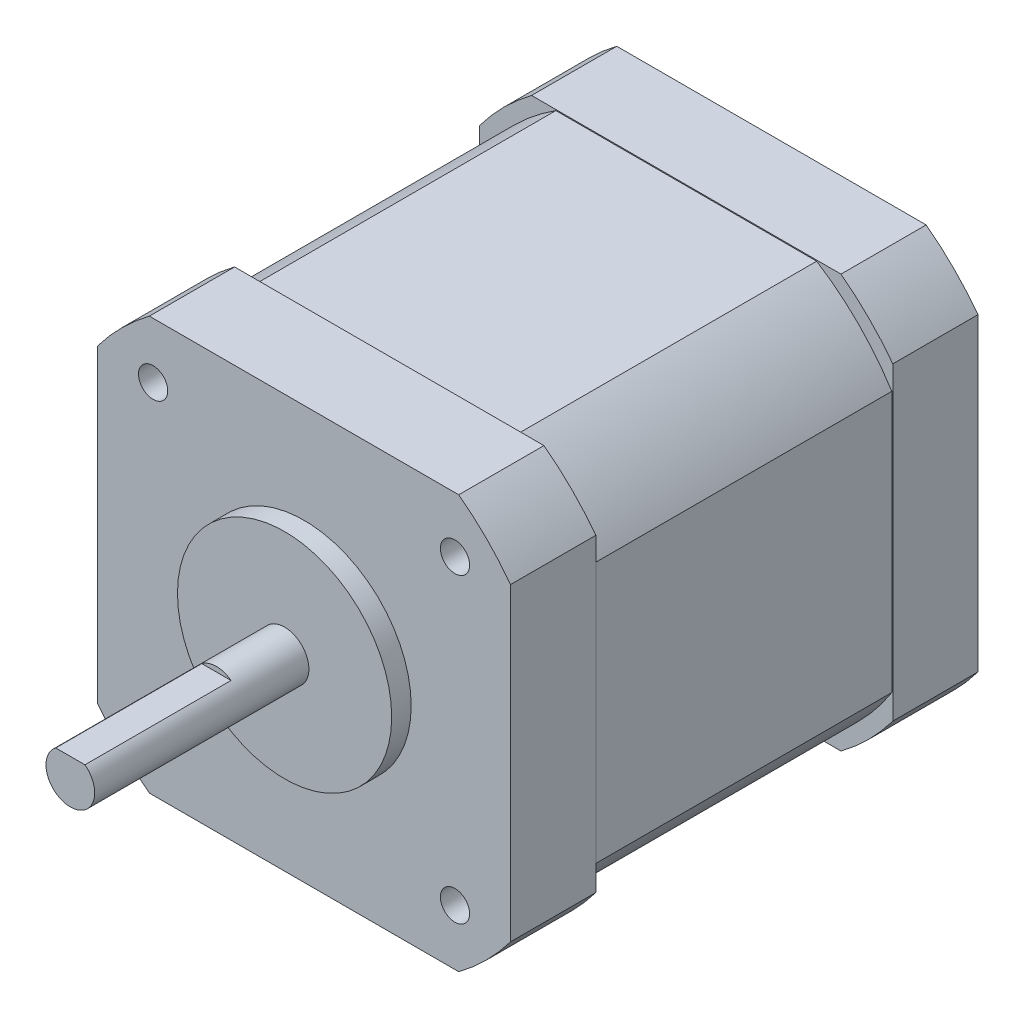
SolidWorks part; units mm, degrees
material "Plain Carbon Steel"
ref_plane "Front" through (0, 0, 0) normal (0, 0, 1) x (1, 0, 0)
ref_plane "Top" through (0, 0, 0) normal (0, 1, 0) x (1, 0, 0)
ref_plane "Right" through (0, 0, 0) normal (1, 0, 0) x (0, 0, -1)
sketch "Sketch1" plane through (0, 0, 0) normal (0, 0, 1) x (1, 0, 0)
  circle A0 centre (0, 0) radius 2.5
  dimension "D1" = 5
extrude "Boss-Extrude1" add sketch "Sketch1" along normal blind 24
sketch "Sketch2" plane through (0, 0, 0) normal (0, 0, -1) x (-1, 0, 0)
  circle A0 centre (0, 0) radius 11
  dimension "D1" = 22
extrude "Boss-Extrude2" add sketch "Sketch2" against normal blind 2
sketch "Sketch3" plane through (0, 0, 0) normal (0, 0, -1) x (-1, 0, 0)
  line L1 (21.209, -21.209) -> (-21.209, -21.209)
  line L2 (21.209, -21.209) -> (21.209, 21.209)
  line L3 (21.209, 21.209) -> (-21.209, 21.209)
  line L4 (-21.209, -21.209) -> (-21.209, 21.209)
  line L5 (21.209, -21.209) -> (-21.209, 21.209) construction
  line L6 (21.209, 21.209) -> (-21.209, -21.209) construction
  point P0 (0, 0)
  dimension "D1" = 42.418
extrude "Boss-Extrude3" add sketch "Sketch3" along normal blind 48
sketch "Sketch4" plane through (0, 0, -48) normal (0, 0, -1) x (-1, 0, 0)
  line L0 (-21.209, -15.888) -> (-21.209, -21.209)
  line L1 (15.888, -21.209) -> (21.209, -21.209)
  line L2 (21.209, 15.888) -> (21.209, 21.209)
  line L3 (-15.888, 21.209) -> (-21.209, 21.209)
  line L4 (-21.209, 21.209) -> (-21.209, -21.209)
  line L5 (-21.209, -21.209) -> (21.209, -21.209)
  line L6 (21.209, -21.209) -> (21.209, 21.209)
  line L7 (21.209, 21.209) -> (-21.209, 21.209)
  line L8 (-21.209, 21.209) -> (-21.209, 15.888)
  line L9 (-21.209, -21.209) -> (-15.888, -21.209)
  line L10 (21.209, -21.209) -> (21.209, -15.888)
  line L11 (21.209, 21.209) -> (15.888, 21.209)
  arc A0 (-21.209, -15.888) -> (-15.888, -21.209) centre (0, 0) ccw
  arc A1 (15.888, -21.209) -> (21.209, -15.888) centre (0, 0) ccw
  arc A2 (21.209, 15.888) -> (15.888, 21.209) centre (0, 0) ccw
  arc A3 (-15.888, 21.209) -> (-21.209, 15.888) centre (0, 0) ccw
  dimension "D2" = 26.5
  dimension "D1" = 0
extrude "Cut-Extrude1" cut sketch "Sketch4" against normal through all
hole_wizard "M3x0.5 Tapped Hole1" positions "Sketch6" profile "Sketch5" tap size "M3x0.5" standard "ANSI Metric"
sketch "Sketch6" plane through (0, 0, 0) normal (0, 0, 1) x (1, 0, 0)
  line L0 (-16.1632, 0) -> (0, 0) construction
  line L1 (0, 0) -> (0, 15.0764) construction
  point P0 (-15.5, 15.5)
  point P11 (-15.5, -15.5)
  point P12 (15.5, -15.5)
  point P13 (15.5, 15.5)
  dimension "D1" = 31
  dimension "D2" = 31
sketch "Sketch5" plane through (-15.5, 15.5, 0) normal (1, 0, 0) x (0, -1, 0)
  line L0 (0, 0) -> (0, 8.2511)
  line L1 (0, 8.2511) -> (1.25, 7.5)
  line L2 (1.25, 7.5) -> (1.25, 6)
  line L3 (1.25, 6) -> (1.5, 6)
  line L4 (1.5, 6) -> (1.5, 0)
  line L5 (1.5, 0) -> (0, 0)
  line L10 (0, 8.2511) -> (-1.25, 7.5) construction
  line L11 (0, -6.35) -> (0, 107.95) construction
  dimension "Tap Drill Dia." = 2.5
  dimension "Tap Drill Depth" = 7.5
  dimension "Thread Major Dia." = 3
  dimension "Thread Depth" = 6
  dimension "Drill Angle" = 118
sketch "Sketch7" plane through (0, 0, 24) normal (0, 0, 1) x (1, 0, 0)
  line L0 (-1.5, 2) -> (1.5, 2)
  circle A0 centre (0, 0) radius 2.5 construction
  circle A1 centre (0, 0) radius 2.5 construction
  arc A2 (1.5, 2) -> (-1.5, 2) centre (0, 0) ccw
  dimension "D1" = 4.5
extrude "Cut-Extrude2" cut sketch "Sketch7" against normal blind 15
ref_plane "Plane1" through (0, 0, -24) normal (0, 0, 1) x (1, 0, 0)
sketch "Sketch8" plane through (0, 0, -24) normal (0, 0, 1) x (1, 0, 0)
  line L0 (-13.3944, 21.109) -> (13.3944, 21.109)
  line L1 (-5.7152, 0) -> (0, 0) construction
  line L2 (0, 0) -> (0, 8.4579) construction
  line L3 (-15.888, 21.209) -> (15.888, 21.209) construction
  line L4 (-13.3944, -21.109) -> (13.3944, -21.109)
  line L5 (-21.109, 13.3944) -> (-21.109, -13.3944)
  line L6 (-21.209, -15.888) -> (-21.209, 15.888) construction
  line L7 (21.109, 13.3944) -> (21.109, -13.3944)
  line L12 (15.888, 21.209) -> (-15.888, 21.209)
  line L13 (-21.209, 15.888) -> (-21.209, -15.888)
  line L14 (-15.888, -21.209) -> (15.888, -21.209)
  line L15 (21.209, -15.888) -> (21.209, 15.888)
  line L16 (15.888, 21.209) -> (-15.888, 21.209)
  line L17 (-21.209, 15.888) -> (-21.209, -15.888)
  line L18 (-15.888, -21.209) -> (15.888, -21.209)
  line L19 (21.209, -15.888) -> (21.209, 15.888)
  arc A0 (-13.3944, 21.109) -> (-21.109, 13.3944) centre (0, 0) ccw
  arc A1 (-21.109, -13.3944) -> (-13.3944, -21.109) centre (0, 0) ccw
  arc A2 (21.109, 13.3944) -> (13.3944, 21.109) centre (0, 0) ccw
  arc A3 (13.3944, -21.109) -> (21.109, -13.3944) centre (0, 0) ccw
  arc A5 (-15.888, 21.209) -> (-21.209, 15.888) centre (0, 0) ccw
  arc A6 (-21.209, -15.888) -> (-15.888, -21.209) centre (0, 0) ccw
  arc A7 (15.888, -21.209) -> (21.209, -15.888) centre (0, 0) ccw
  arc A8 (21.209, 15.888) -> (15.888, 21.209) centre (0, 0) ccw
  arc A9 (-15.888, 21.209) -> (-21.209, 15.888) centre (0, 0) ccw
  arc A10 (-21.209, -15.888) -> (-15.888, -21.209) centre (0, 0) ccw
  arc A11 (15.888, -21.209) -> (21.209, -15.888) centre (0, 0) ccw
  arc A12 (21.209, 15.888) -> (15.888, 21.209) centre (0, 0) ccw
  dimension "D1" = 50
  dimension "D2" = 0.1
  dimension "D3" = 0.1
  dimension "D4" = 0
extrude "Cut-Extrude3" cut sketch "Sketch8" against normal mid plane 30.5
